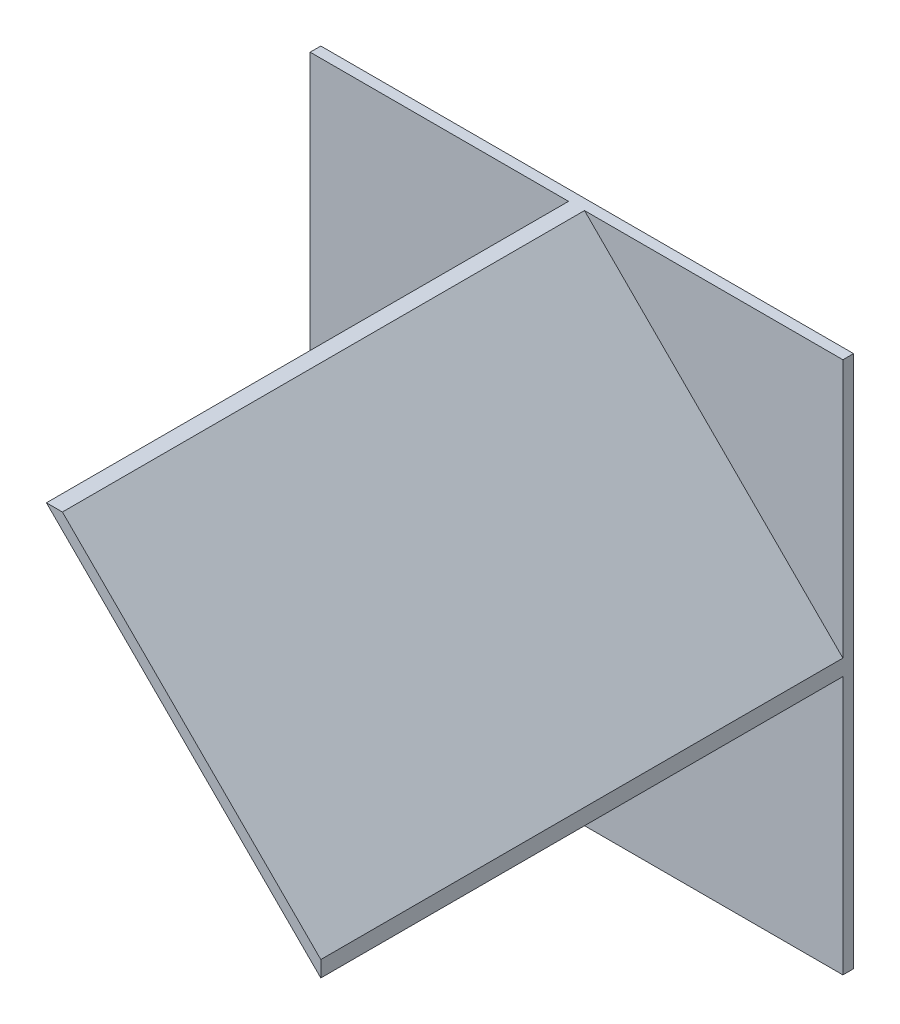
SolidWorks part; units mm, degrees
ref_plane "Płaszczyzna przednia" through (0, 0, 0) normal (0, 0, 1) x (1, 0, 0)
ref_plane "Płaszczyzna górna" through (0, 0, 0) normal (0, 1, 0) x (1, 0, 0)
ref_plane "Płaszczyzna prawa" through (0, 0, 0) normal (1, 0, 0) x (0, 0, -1)
sketch "Szkic1" plane through (0, 0, 0) normal (0, 0, 1) x (1, 0, 0)
  line L0 (0, 0) -> (100, 0)
  line L1 (0, 0) -> (-100, 0)
  line L2 (0, 0) -> (0, 100)
  line L3 (0, 0) -> (0, -100)
  line L4 (0, 100) -> (100, 100)
  line L5 (100, 100) -> (100, 0)
  line L6 (100, -100) -> (0, -100)
  line L7 (100, 0) -> (100, -100)
  line L8 (0, 100) -> (-100, 100)
  line L9 (-100, 100) -> (-100, 0)
  line L10 (-100, -100) -> (-100, 0)
  line L11 (0, -100) -> (-100, -100)
  dimension "D1" = 100
  dimension "D2" = 100
  dimension "D3" = 100
  dimension "D4" = 100
  dimension "D5" = 100
  dimension "D6" = 100
  dimension "D7" = 100
  dimension "D8" = 100
  dimension "D9" = 100
  dimension "D10" = 100
  dimension "D11" = 100
extrude "Dodanie-wyciągnięcie1" add sketch "Szkic1" along normal blind 4 contours L8 L9 L1 L2 | L5 L4 L2 L0 | L7 L0 L3 L6 | L11 L3 L1 L10
sketch "Szkic2" plane through (0, 0, 4) normal (0, 0, 1) x (1, 0, 0)
  line L1 (100, 100) -> (-100, 100) construction
  line L2 (100, -100) -> (-100, -100) construction
  line L9 (-2, -100) -> (2, -100)
  line L24 (0, 100) -> (3, 100)
  line L25 (0, 100) -> (-3, 100)
  line L26 (100, 0) -> (100, 3)
  line L27 (100, 100) -> (100, -100) construction
  line L28 (100, 0) -> (100, -3)
  line L29 (3, 100) -> (100, 3)
  line L30 (-3, 100) -> (100, -3)
  dimension "D1" = 3
  dimension "D2" = 3
  dimension "D3" = 3
  dimension "D4" = 3
  dimension "D8" = 4
extrude "Dodanie-wyciągnięcie4" add sketch "Szkic2" along normal blind 196
